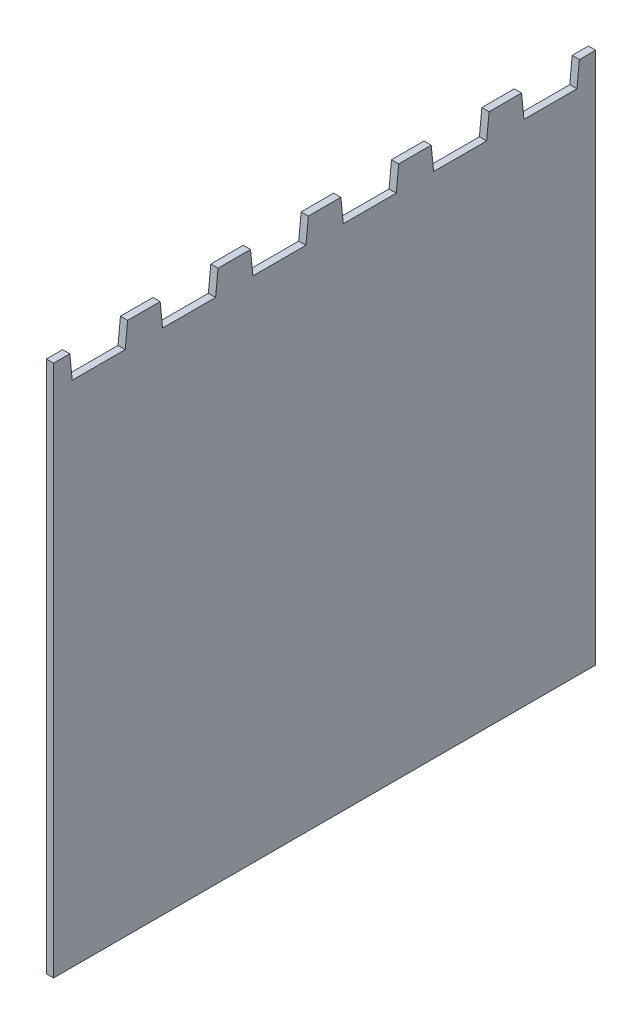
SolidWorks part; units mm, degrees
ref_plane "Front Plane" through (0, 0, 0) normal (0, 0, 1) x (1, 0, 0)
ref_plane "Top Plane" through (0, 0, 0) normal (0, 1, 0) x (1, 0, 0)
ref_plane "Right Plane" through (0, 0, 0) normal (1, 0, 0) x (0, 0, -1)
sketch "Sketch2" plane through (0, 0, 0) normal (1, 0, 0) x (0, 0, -1)
  line L0 (-18.75, 103) -> (-18.75, 118)
  line L1 (-18.75, -103) -> (18.75, -103)
  line L2 (-18.75, -103) -> (-18.75, 103)
  line L3 (-18.75, 103) -> (18.75, 103)
  line L4 (18.75, -103) -> (18.75, 103)
  line L5 (-18.75, -103) -> (18.75, 103) construction
  line L6 (-18.75, 103) -> (18.75, -103) construction
  line L7 (-18.75, 118) -> (-12, 118)
  line L8 (-12, 118) -> (-11, 108)
  line L9 (-11, 108) -> (11, 108)
  line L10 (11, 108) -> (12, 118)
  line L11 (12, 118) -> (18.75, 118)
  line L12 (18.75, 118) -> (18.75, 103)
  line L13 (-12, 118) -> (-12, 108) construction
  line L14 (-12, 108) -> (-11, 108) construction
  line L15 (11, 108) -> (12, 108) construction
  line L16 (12, 108) -> (12, 118) construction
  line L17 (-18.75, 118) -> (-18.75, 125) construction
  line L18 (-18.75, 125) -> (18.75, 125) construction
  line L19 (18.75, 125) -> (18.75, 118) construction
  point P0 (0, 0)
  dimension "D1" = 206
  dimension "D2" = 37.5
  dimension "D3" = 22
  dimension "D4" = 10
  dimension "D5" = 1
  dimension "D6" = 7
  dimension "D7" = 228
extrude "Boss-Extrude2" add sketch "Sketch2" along normal blind 3 contours L1 L4 L3 L2 | L12 L11 L10 L9 L8 L7 L0 L3
pattern_linear "LPattern1" count 6 spacing 37.5 along (0, 0, 1) of "Boss-Extrude2"
